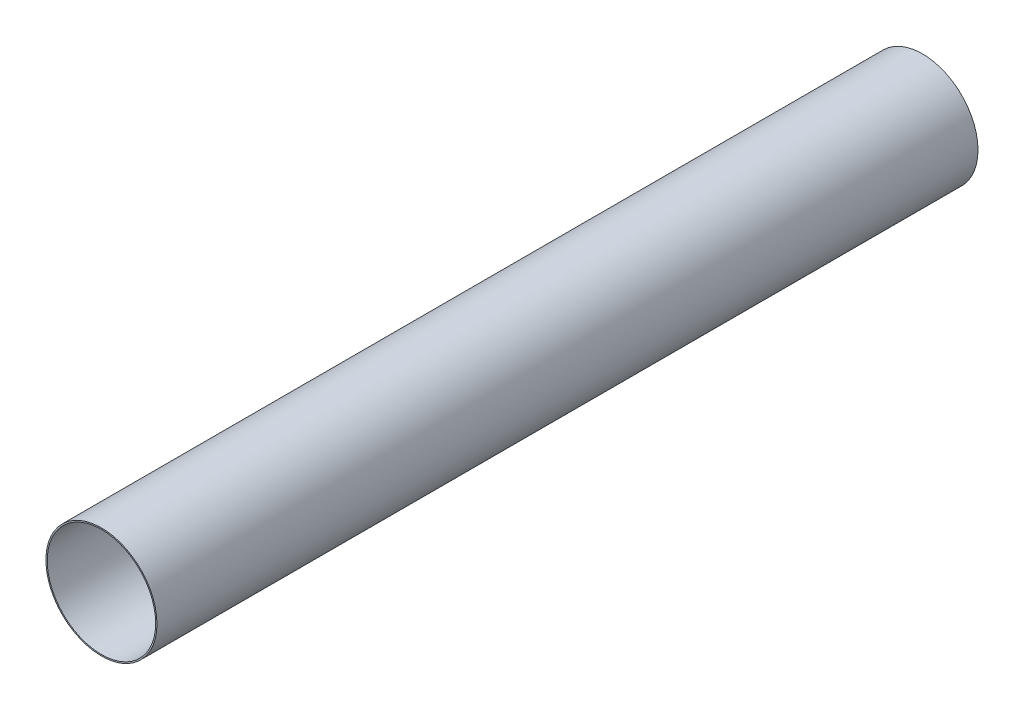
SolidWorks part; units mm, degrees
material "Thornel Mat VMA"
ref_plane "Front Plane" through (0, 0, 0) normal (0, 0, 1) x (1, 0, 0)
ref_plane "Top Plane" through (0, 0, 0) normal (0, 1, 0) x (1, 0, 0)
ref_plane "Right Plane" through (0, 0, 0) normal (1, 0, 0) x (0, 0, -1)
sketch "Sketch1" plane through (0, 0, 0) normal (0, 0, 1) x (1, 0, 0)
  circle A0 centre (0, 0) radius 84.55
  circle A1 centre (0, 0) radius 82.55
  dimension "D1" = 165.1
  dimension "D2" = 169.1
extrude "Boss-Extrude1" add sketch "Sketch1" along normal mid plane 1250
equation "\"TubeDiameter\" = 6.500in"
equation "\"D1@Sketch1\"=\"TubeDiameter\""
equation "\"D2@Sketch1\"=\"TubeDiameter\"+4mm"
